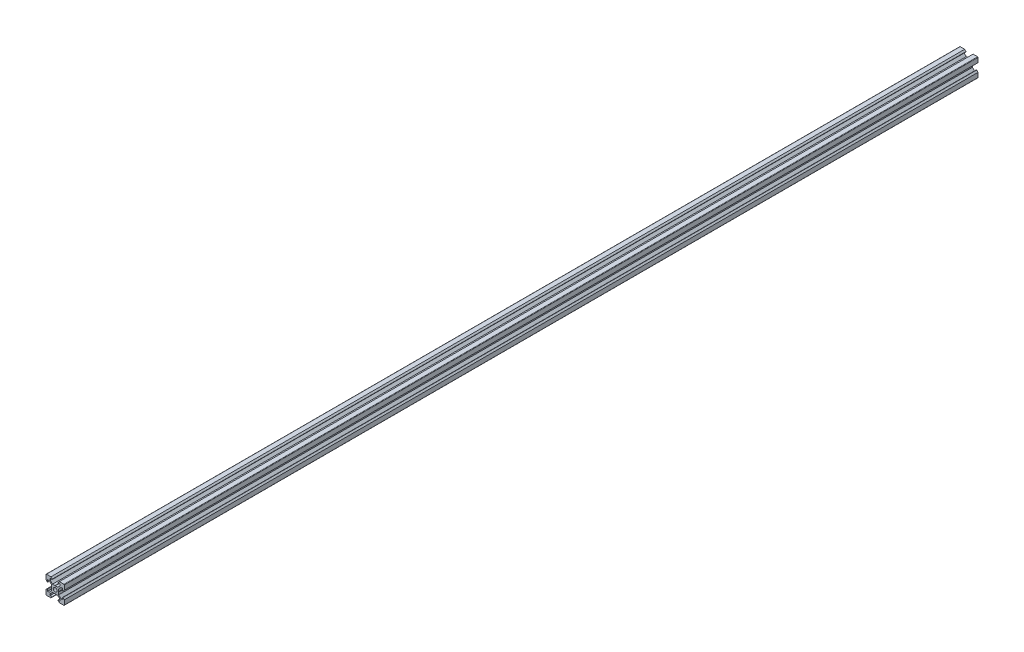
SolidWorks part; units mm, degrees
material "6061-T6 (SS)"
ref_plane "Front Plane" through (0, 0, 0) normal (0, 0, 1) x (1, 0, 0)
ref_plane "Top Plane" through (0, 0, 0) normal (0, 1, 0) x (1, 0, 0)
ref_plane "Right Plane" through (0, 0, 0) normal (1, 0, 0) x (0, 0, -1)
sketch "Sketch1" plane through (0, 0, 0) normal (0, 0, 1) x (1, 0, 0)
  line L1 (9.5, -10) -> (-9.5, -10)
  line L2 (10, -9.5) -> (10, 9.5)
  line L3 (9.5, 10) -> (-9.5, 10)
  line L4 (-10, -9.5) -> (-10, 9.5)
  line L5 (10, -10) -> (-10, 10) construction
  line L6 (10, 10) -> (-10, -10) construction
  circle A0 centre (0, 0) radius 2.1
  arc A1 (-9.5, 10) -> (-10, 9.5) centre (-9.5, 9.5) ccw
  arc A2 (10, 9.5) -> (9.5, 10) centre (9.5, 9.5) ccw
  arc A3 (9.5, -10) -> (10, -9.5) centre (9.5, -9.5) ccw
  arc A4 (-9.5, -10) -> (-10, -9.5) centre (-9.5, -9.5) cw
  point P0 (0, 0)
  line B0 (0, 0) -> (0, 10) construction
  line B1 (0, 3.69) -> (-0.21, 3.9)
  line B2 (-0.21, 3.9) -> (-2.8393, 3.9)
  line B3 (-2.8393, 3.9) -> (-5.5, 6.5607)
  line B4 (-5.5, 6.5607) -> (-5.5, 8.2)
  line B5 (-5.5, 8.2) -> (-3.125, 8.2)
  line B6 (-3.125, 8.2) -> (-3.125, 8.545)
  line B7 (-3.125, 8.545) -> (-4.58, 10)
  line B8 (-4.58, 10) -> (4.58, 10)
  line B9 (0, 0) -> (-5.9132, 5.9132) construction
  line B10 (3.125, 8.545) -> (4.58, 10)
  line B11 (3.125, 8.2) -> (3.125, 8.545)
  line B12 (5.5, 8.2) -> (3.125, 8.2)
  line B13 (5.5, 6.5607) -> (5.5, 8.2)
  line B14 (2.8393, 3.9) -> (5.5, 6.5607)
  line B15 (0.21, 3.9) -> (2.8393, 3.9)
  line B16 (0, 3.69) -> (0.21, 3.9)
  line B17 (0, 0) -> (-10, 0) construction
  line B18 (-3.69, 0) -> (-3.9, -0.21)
  line B19 (-3.9, -0.21) -> (-3.9, -2.8393)
  line B20 (-3.9, -2.8393) -> (-6.5607, -5.5)
  line B21 (-6.5607, -5.5) -> (-8.2, -5.5)
  line B22 (-8.2, -5.5) -> (-8.2, -3.125)
  line B23 (-8.2, -3.125) -> (-8.545, -3.125)
  line B24 (-8.545, -3.125) -> (-10, -4.58)
  line B25 (-10, -4.58) -> (-10, 4.58)
  line B26 (0, 0) -> (-5.9132, -5.9132) construction
  line B27 (-8.545, 3.125) -> (-10, 4.58)
  line B28 (-8.2, 3.125) -> (-8.545, 3.125)
  line B29 (-8.2, 5.5) -> (-8.2, 3.125)
  line B30 (-6.5607, 5.5) -> (-8.2, 5.5)
  line B31 (-3.9, 2.8393) -> (-6.5607, 5.5)
  line B32 (-3.9, 0.21) -> (-3.9, 2.8393)
  line B33 (-3.69, 0) -> (-3.9, 0.21)
  line B34 (0, 0) -> (0, -10) construction
  line B35 (0, -3.69) -> (0.21, -3.9)
  line B36 (0.21, -3.9) -> (2.8393, -3.9)
  line B37 (2.8393, -3.9) -> (5.5, -6.5607)
  line B38 (5.5, -6.5607) -> (5.5, -8.2)
  line B39 (5.5, -8.2) -> (3.125, -8.2)
  line B40 (3.125, -8.2) -> (3.125, -8.545)
  line B41 (3.125, -8.545) -> (4.58, -10)
  line B42 (4.58, -10) -> (-4.58, -10)
  line B43 (0, 0) -> (5.9132, -5.9132) construction
  line B44 (-3.125, -8.545) -> (-4.58, -10)
  line B45 (-3.125, -8.2) -> (-3.125, -8.545)
  line B46 (-5.5, -8.2) -> (-3.125, -8.2)
  line B47 (-5.5, -6.5607) -> (-5.5, -8.2)
  line B48 (-2.8393, -3.9) -> (-5.5, -6.5607)
  line B49 (-0.21, -3.9) -> (-2.8393, -3.9)
  line B50 (0, -3.69) -> (-0.21, -3.9)
  line B51 (0, 0) -> (10, 0) construction
  line B52 (3.69, 0) -> (3.9, 0.21)
  line B53 (3.9, 0.21) -> (3.9, 2.8393)
  line B54 (3.9, 2.8393) -> (6.5607, 5.5)
  line B55 (6.5607, 5.5) -> (8.2, 5.5)
  line B56 (8.2, 5.5) -> (8.2, 3.125)
  line B57 (8.2, 3.125) -> (8.545, 3.125)
  line B58 (8.545, 3.125) -> (10, 4.58)
  line B59 (10, 4.58) -> (10, -4.58)
  line B60 (0, 0) -> (5.9132, 5.9132) construction
  line B61 (8.545, -3.125) -> (10, -4.58)
  line B62 (8.2, -3.125) -> (8.545, -3.125)
  line B63 (8.2, -5.5) -> (8.2, -3.125)
  line B64 (6.5607, -5.5) -> (8.2, -5.5)
  line B65 (3.9, -2.8393) -> (6.5607, -5.5)
  line B66 (3.9, -0.21) -> (3.9, -2.8393)
  line B67 (3.69, 0) -> (3.9, -0.21)
  dimension "D1" = 4.2
  dimension "D3" = 0.5
  dimension "D2" = 20
sketch_block_instance "V Slot 1-4"
sketch_block "V Slot 1" parameters "D1"=10, "D2"=11, "D3"=4.3, "D4"=1.8, "D5"=0.21, "D6"=45, "D7"=9.16, "D8"=1.5, "D9"=6.25
sketch_block_instance "V Slot 1-5"
sketch_block_instance "V Slot 1-6"
sketch_block_instance "V Slot 1-7"
extrude "Boss-Extrude1" add sketch "Sketch1" along normal mid plane 1000 contours B67 B52 B53 B54 B55 B56 B57 B58 L2 A2 L3 B10 B11 B12 B13 B14 B15 B16 B1 B2 B3 B4 B5 B6 B7 A1 L4 B27 B28 B29 B30 B31 B32 B33 B18 B19 B20 B21 B22 B23 B24 A4 L1 B44 B45 B46 B47 B48 B49
